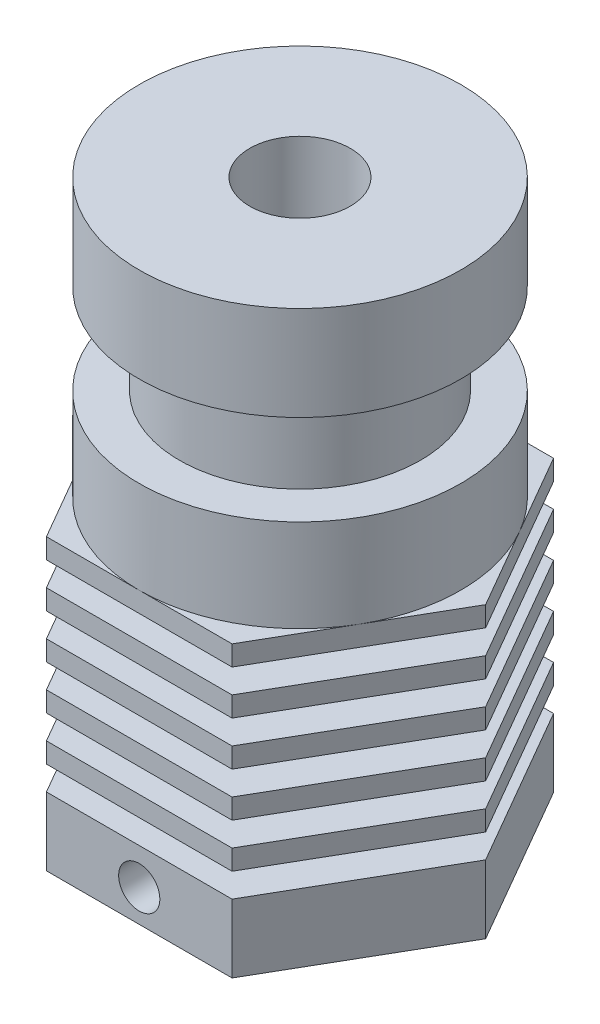
SolidWorks part; units mm, degrees
material "6061-T6 (SS)"
ref_plane "Front Plane" through (0, 0, 0) normal (0, 0, 1) x (1, 0, 0)
ref_plane "Top Plane" through (0, 0, 0) normal (0, 1, 0) x (1, 0, 0)
ref_plane "Right Plane" through (0, 0, 0) normal (1, 0, 0) x (0, 0, -1)
sketch "Sketch1" plane through (0, 0, 0) normal (0, 0, 1) x (1, 0, 0)
  line L0 (0, 0) -> (0, 32.0593) construction
  line L1 (3, 0) -> (3, 3.2)
  line L2 (3, 3.2) -> (2.05, 3.2)
  line L3 (2.05, 3.2) -> (2.05, 28.2)
  line L4 (2.05, 28.2) -> (8, 28.2)
  line L5 (8, 28.2) -> (8, 23.5)
  line L6 (8, 23.5) -> (6, 23.5)
  line L7 (6, 23.5) -> (6, 19)
  line L8 (6, 19) -> (8, 19)
  line L9 (8, 19) -> (8, 14.4)
  line L10 (8, 14.4) -> (14.3078, 14.4)
  line L11 (14.3078, 14.4) -> (14.3078, 13.4)
  line L12 (14.3078, 13.4) -> (4.75, 13.4)
  line L13 (4.75, 13.4) -> (4.75, 12.2)
  line L14 (4.75, 12.2) -> (14.3078, 12.2)
  line L15 (14.3078, 12.2) -> (14.3078, 11.2)
  line L16 (14.3078, 11.2) -> (4.75, 11.2)
  line L17 (4.75, 11.2) -> (4.75, 10)
  line L18 (4.75, 10) -> (14.3078, 10)
  line L19 (14.3078, 10) -> (14.3078, 9)
  line L20 (14.3078, 9) -> (4.75, 9)
  line L21 (4.75, 9) -> (4.75, 7.8)
  line L22 (4.75, 7.8) -> (14.3078, 7.8)
  line L23 (14.3078, 7.8) -> (14.3078, 6.8)
  line L24 (14.3078, 6.8) -> (4.75, 6.8)
  line L25 (4.75, 6.8) -> (4.75, 5.6)
  line L26 (4.75, 5.6) -> (14.3078, 5.6)
  line L27 (14.3078, 5.6) -> (14.3078, 4.6)
  line L28 (14.3078, 4.6) -> (4.75, 4.6)
  line L29 (4.75, 4.6) -> (4.75, 3.4)
  line L30 (4.75, 3.4) -> (14.3078, 3.4)
  line L31 (14.3078, 3.4) -> (14.3078, 0)
  line L32 (14.3078, 0) -> (3, 0)
  dimension "D1" = 1.2
  dimension "D2" = 1
  dimension "D3" = 4.1
  dimension "D4" = 6
  dimension "D5" = 3.2
  dimension "D6" = 3.4
  dimension "D7" = 4.6
  dimension "D8" = 4.7
  dimension "D9" = 4.5
  dimension "D10" = 16
  dimension "D11" = 12
  dimension "D12" = 9.5
  dimension "D13" = 28.6155
revolve "Revolve1" add sketch "Sketch1" angle 360 about L0
sketch "Sketch2" plane through (0, 14.4, 0) normal (0, 1, 0) x (1, 0, 0)
  line L1 (-4.6188, 8) -> (-9.2376, 0)
  line L2 (-9.2376, 0) -> (-4.6188, -8)
  line L3 (-4.6188, -8) -> (4.6188, -8)
  line L4 (4.6188, -8) -> (9.2376, 0)
  line L5 (9.2376, 0) -> (4.6188, 8)
  line L6 (4.6188, 8) -> (-4.6188, 8)
  circle A0 centre (0, 0) radius 8 construction
  dimension "D1" = 16
extrude "Cut-Extrude1" cut sketch "Sketch2" against normal through all flip side to cut
hole_wizard "M6x1.0 Tapped Hole1" positions "Sketch4" profile "Sketch3" tap size "M6x1.0" standard "Ansi Metric"
sketch "Sketch4" plane through (0, 28.2, 0) normal (0, 1, 0) x (-1, 0, 0)
  point P0 (0, 0)
sketch "Sketch3" plane through (0, 28.2, 0) normal (1, 0, 0) x (0, 0, 1)
  line L0 (0, 0) -> (0, 6.5022)
  line L1 (0, 6.5022) -> (2.5, 5)
  line L2 (2.5, 5) -> (2.5, 0)
  line L5 (2.5, 0) -> (0, 0)
  line L10 (0, 6.5022) -> (-2.5, 5) construction
  line L11 (0, -6.35) -> (0, 107.95) construction
  dimension "Tap Drill Dia." = 5
  dimension "Tap Drill Depth" = 5
  dimension "Drill Angle" = 118
cosmetic thread "Hole Thread1" parameters "D1"=4.5, "D2"=6
hole_wizard "M2.5x0.45 Tapped Hole1" positions "Sketch6" profile "Sketch5" tap size "M2.5x0.45" standard "Ansi Metric"
sketch "Sketch6" plane through (0, 0, 8) normal (0, 0, 1) x (1, 0, 0)
  line L0 (-4.6188, 0) -> (4.6188, 0) construction
  point P0 (0, 1.6)
  dimension "D1" = 1.6
sketch "Sketch5" plane through (0, 1.6, 8) normal (1, 0, 0) x (0, -1, 0)
  line L0 (0, 0) -> (0, 9.6159)
  line L1 (0, 9.6159) -> (1.025, 9)
  line L2 (1.025, 9) -> (1.025, 0)
  line L5 (1.025, 0) -> (0, 0)
  line L10 (0, 9.6159) -> (-1.025, 9) construction
  line L11 (0, -6.35) -> (0, 107.95) construction
  dimension "Tap Drill Dia." = 2.05
  dimension "Tap Drill Depth" = 9
  dimension "Drill Angle" = 118
cosmetic thread "Hole Thread2" parameters "D1"=5.1805, "D2"=2.5
